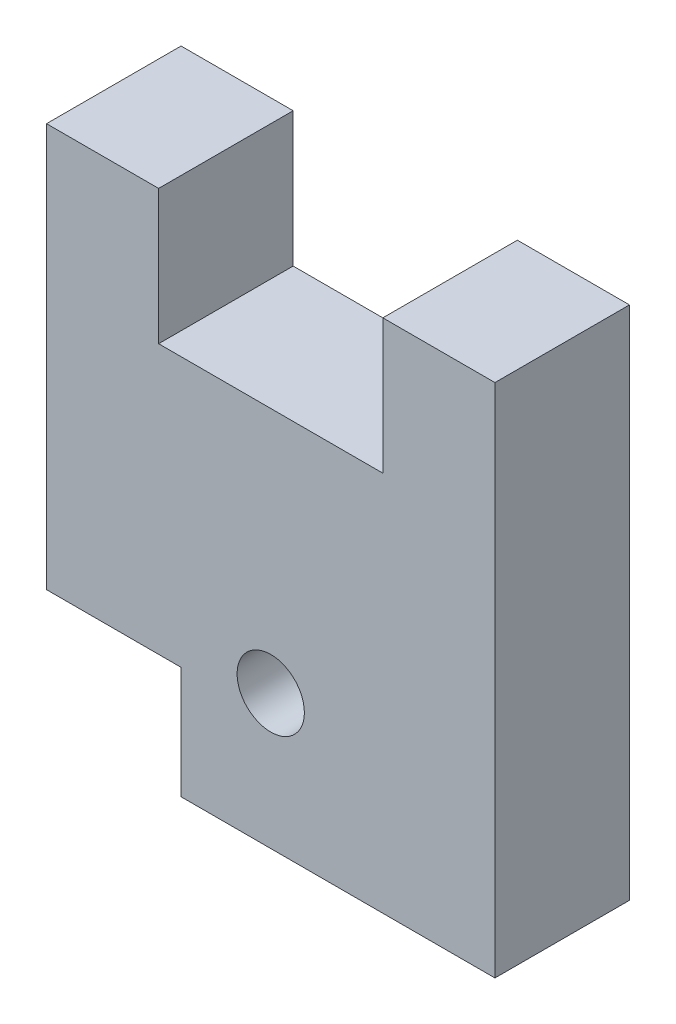
SolidWorks part; units mm, degrees
material "Acrylic (Medium-high impact)"
ref_plane "Front Plane" through (0, 0, 0) normal (0, 0, 1) x (1, 0, 0)
ref_plane "Top Plane" through (0, 0, 0) normal (0, 1, 0) x (1, 0, 0)
ref_plane "Right Plane" through (0, 0, 0) normal (1, 0, 0) x (0, 0, -1)
sketch "Sketch1" plane through (0, 0, 0) normal (0, 0, 1) x (1, 0, 0)
  line L0 (15, 0) -> (20, 0)
  line L1 (0, 0) -> (5, 0)
  line L2 (0, 0) -> (0, -18)
  line L3 (6, -23) -> (20, -23)
  line L4 (20, 0) -> (20, -23)
  line L6 (5, 0) -> (5, -6)
  line L7 (5, -6) -> (15, -6)
  line L8 (15, 0) -> (15, -6)
  line L16 (0, -18) -> (6, -18)
  line L17 (6, -23) -> (6, -18)
  circle A0 centre (10, -17) radius 1.5
  point P13 (10, -6)
  dimension "D6" = 3
  dimension "D7" = 11
  dimension "D1" = 5
  dimension "D2" = 5
  dimension "D3" = 10
  dimension "D4" = 6
  dimension "D5" = 23
  dimension "D8" = 6
  dimension "D9" = 5
extrude "Boss-Extrude1" add sketch "Sketch1" along normal blind 6
